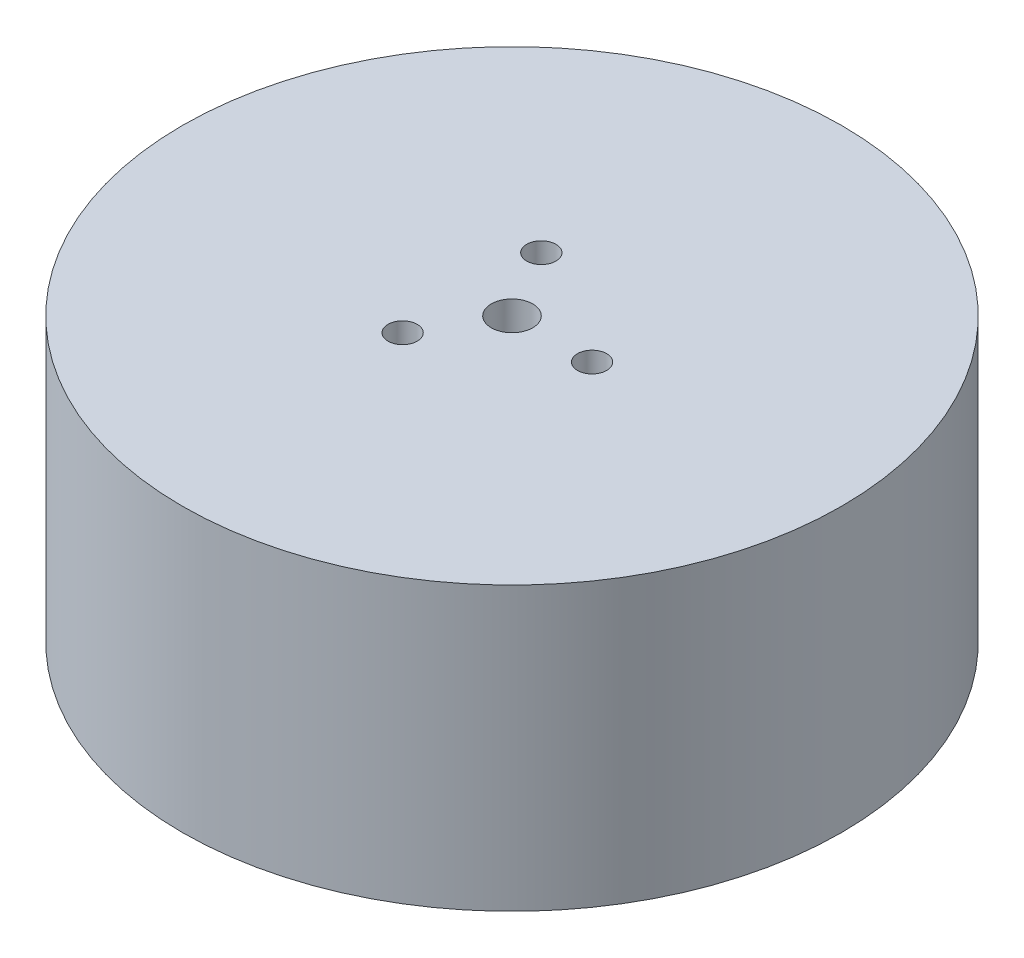
SolidWorks part; units mm, degrees
ref_plane "前视基准面" through (0, 0, 0) normal (0, 0, 1) x (1, 0, 0)
ref_plane "上视基准面" through (0, 0, 0) normal (0, 1, 0) x (1, 0, 0)
ref_plane "右视基准面" through (0, 0, 0) normal (1, 0, 0) x (0, 0, -1)
sketch "草图1" plane through (0, 0, 0) normal (0, 1, 0) x (1, 0, 0)
  circle A0 centre (0, 0) radius 35
extrude "凸台-拉伸1" add sketch "草图1" along normal blind 30
sketch "草图2" plane through (0, 0, 0) normal (0, -1, 0) x (1, 0, 0)
  circle A0 centre (0, 0) radius 23.2
extrude "切除-拉伸1" cut sketch "草图2" against normal blind 26
sketch "草图3" plane through (0, 30, 0) normal (0, 1, 0) x (1, 0, 0)
  circle A0 centre (0, 0) radius 2.2
  circle A1 centre (0, 0) radius 8.5
  circle A2 centre (8.5, 0) radius 1.55
  circle A3 centre (-4.25, -7.3612) radius 1.55
  circle A4 centre (-4.25, 7.3612) radius 1.55
  point P13 (0, 0)
  dimension "D1" = 3
extrude "切除-拉伸2" cut sketch "草图3" against normal up to next contours A4 | A3 | A0 | A2
